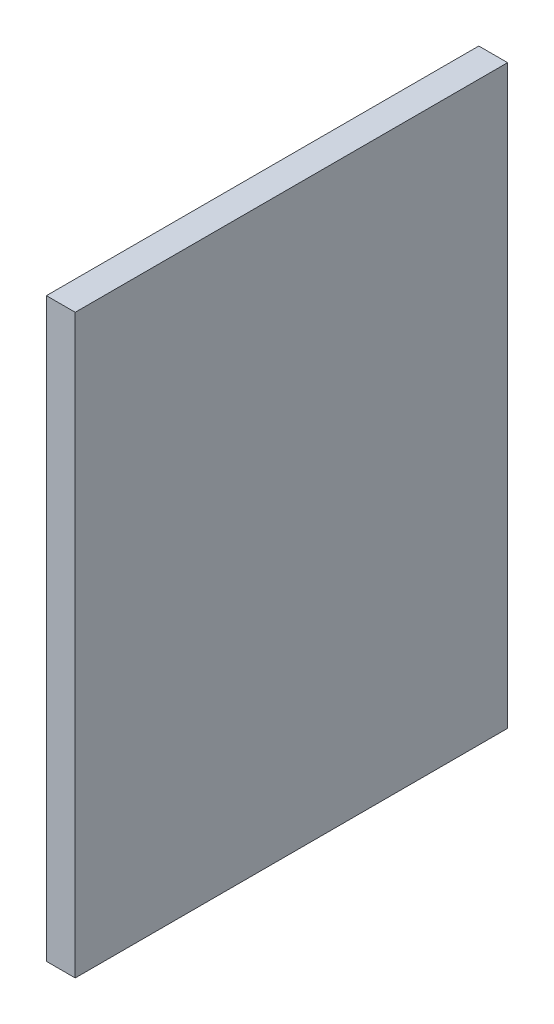
SolidWorks part; units mm, degrees
ref_plane "Спереди" through (0, 0, 0) normal (0, 0, 1) x (1, 0, 0)
ref_plane "Сверху" through (0, 0, 0) normal (0, 1, 0) x (1, 0, 0)
ref_plane "Справа" through (0, 0, 0) normal (1, 0, 0) x (0, 0, -1)
sketch "Эскиз1" plane through (0, 0, 0) normal (1, 0, 0) x (0, 0, -1)
  line L1 (0, 0) -> (900, 0)
  line L2 (0, 0) -> (0, 1200)
  line L3 (0, 1200) -> (900, 1200)
  line L4 (900, 0) -> (900, 1200)
extrude "Бобышка-Вытянуть1" add sketch "Эскиз1" along normal blind 60
